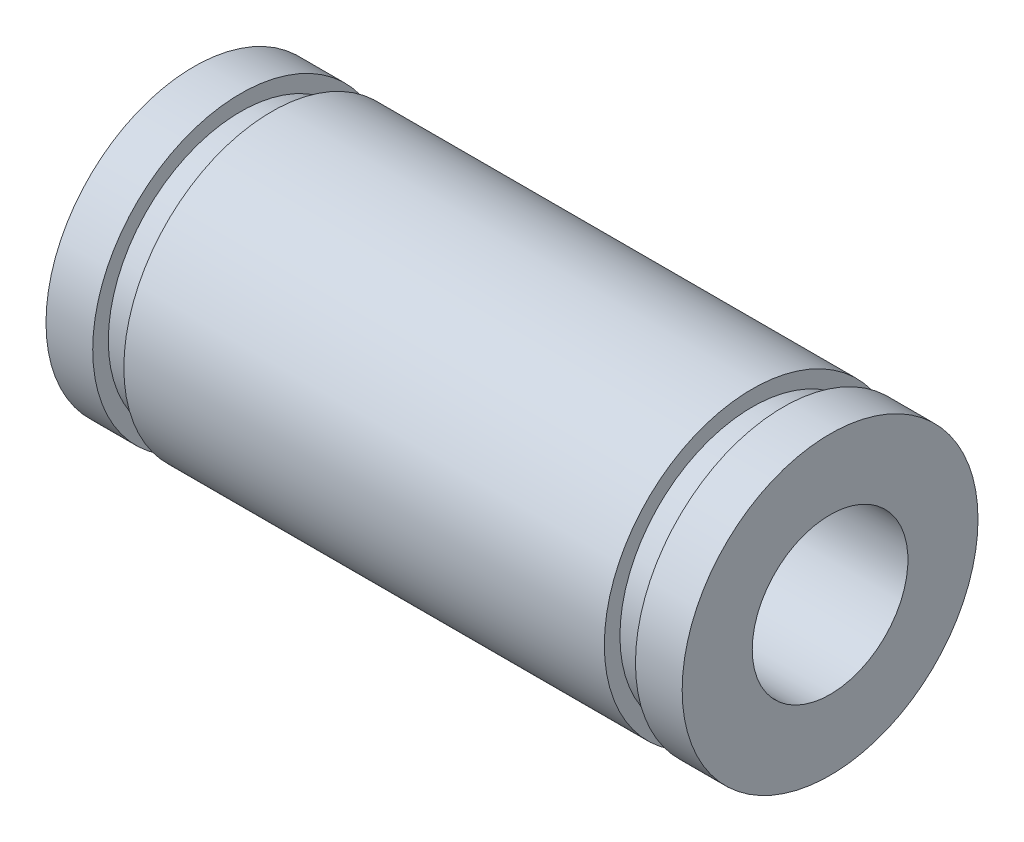
SolidWorks part; units mm, degrees
ref_plane "Front Plane" through (0, 0, 0) normal (0, 0, 1) x (1, 0, 0)
ref_plane "Top Plane" through (0, 0, 0) normal (0, 1, 0) x (1, 0, 0)
ref_plane "Right Plane" through (0, 0, 0) normal (1, 0, 0) x (0, 0, -1)
sketch "Sketch1" plane through (0, 0, 0) normal (0, 0, 1) x (1, 0, 0)
  line L0 (-38.7538, 0) -> (40.2175, 0) construction
  line L1 (-17.9538, 9.5) -> (-14.9538, 9.5)
  line L2 (-17.9538, 5) -> (22.9051, 5)
  line L3 (-17.9538, 9.5) -> (-17.9538, 5)
  line L4 (22.9051, 9.5) -> (22.9051, 5)
  line L5 (-14.9538, 9.5) -> (-14.9538, 8.4976)
  line L6 (-14.9538, 8.4976) -> (-12.9538, 8.4976)
  line L7 (-12.9538, 8.4976) -> (-12.9538, 9.5)
  line L8 (-12.9538, 9.5) -> (17.9051, 9.5)
  line L9 (17.9051, 9.5) -> (17.9051, 8.4976)
  line L10 (17.9051, 8.4976) -> (19.9051, 8.4976)
  line L11 (19.9051, 8.4976) -> (19.9051, 9.5)
  line L12 (19.9051, 9.5) -> (22.9051, 9.5)
  dimension "D1" = 40.8589
  dimension "D2" = 2
  dimension "D3" = 5
  dimension "D4" = 2
  dimension "D5" = 3
  dimension "D6" = 3
revolve "Revolve1" add sketch "Sketch1" angle 360 about L0
